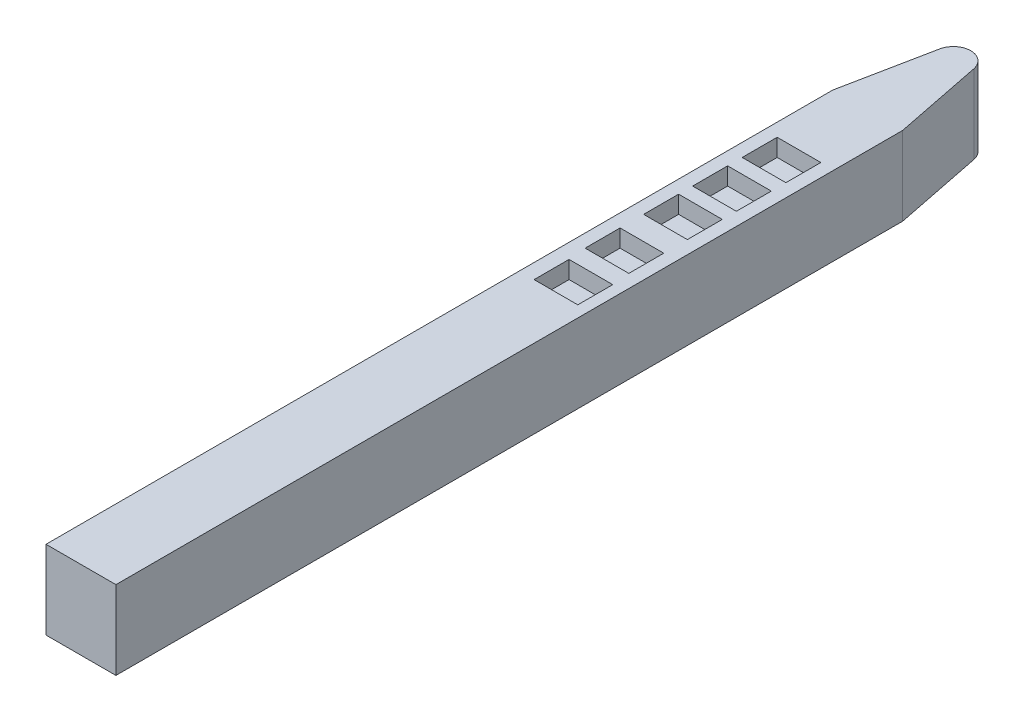
SolidWorks part; units mm, degrees
ref_plane "Front Plane" through (0, 0, 0) normal (0, 0, 1) x (1, 0, 0)
ref_plane "Top Plane" through (0, 0, 0) normal (0, 1, 0) x (1, 0, 0)
ref_plane "Right Plane" through (0, 0, 0) normal (1, 0, 0) x (0, 0, -1)
sketch "Sketch1" plane through (0, 0, 0) normal (0, 1, 0) x (1, 0, 0)
  line L0 (0, 0) -> (0, 1143.3615)
  line L1 (0, 0) -> (101.6, 0)
  line L2 (101.6, 0) -> (101.6, 1143.3615)
  line L3 (0, 1143.3615) -> (50.8, 1397)
  line L4 (50.8, 1397) -> (101.6, 1143.3615)
  line L5 (50.8, 0) -> (50.8, 1705.5122) construction
  dimension "D1" = 1397
  dimension "D2" = 101.6
extrude "Boss-Extrude1" add sketch "Sketch1" along normal blind 114.3
fillet "Fillet2" radius 25.4 1 edges at (50.8, 57.15, -1397)
sketch "Sketch2" plane through (0, 114.3, 0) normal (0, 1, 0) x (1, 0, 0)
  line L0 (50.8, 0) -> (50.8, 1195.0883) construction
  line L1 (0, 0) -> (101.6, 0) construction
  line L2 (19.05, 971.4743) -> (82.55, 971.4743)
  line L3 (19.05, 1043.4464) -> (82.55, 1043.4464)
  line L4 (19.05, 1043.4464) -> (19.05, 992.6464)
  line L5 (19.05, 992.6464) -> (82.55, 992.6464)
  line L6 (82.55, 1043.4464) -> (82.55, 992.6464)
  line L7 (19.05, 1043.4464) -> (82.55, 992.6464) construction
  line L8 (19.05, 992.6464) -> (82.55, 1043.4464) construction
  line L9 (19.05, 971.4743) -> (19.05, 920.6743)
  line L10 (19.05, 920.6743) -> (82.55, 920.6743)
  line L11 (82.55, 971.4743) -> (82.55, 920.6743)
  line L12 (19.05, 971.4743) -> (82.55, 920.6743) construction
  line L13 (19.05, 920.6743) -> (82.55, 971.4743) construction
  line L14 (19.05, 900.2229) -> (82.55, 900.2229)
  line L15 (19.05, 900.2229) -> (19.05, 849.4229)
  line L16 (19.05, 849.4229) -> (82.55, 849.4229)
  line L17 (82.55, 900.2229) -> (82.55, 849.4229)
  line L18 (19.05, 900.2229) -> (82.55, 849.4229) construction
  line L19 (19.05, 849.4229) -> (82.55, 900.2229) construction
  line L20 (19.05, 815.181) -> (82.55, 815.181)
  line L21 (19.05, 815.181) -> (19.05, 764.381)
  line L22 (19.05, 764.381) -> (82.55, 764.381)
  line L23 (82.55, 815.181) -> (82.55, 764.381)
  line L24 (19.05, 815.181) -> (82.55, 764.381) construction
  line L25 (19.05, 764.381) -> (82.55, 815.181) construction
  line L26 (21.5561, 738.5331) -> (85.0561, 738.5331)
  line L27 (21.5561, 738.5331) -> (21.5561, 687.7331)
  line L28 (21.5561, 687.7331) -> (85.0561, 687.7331)
  line L29 (85.0561, 738.5331) -> (85.0561, 687.7331)
  line L30 (21.5561, 738.5331) -> (85.0561, 687.7331) construction
  line L31 (21.5561, 687.7331) -> (85.0561, 738.5331) construction
  point P4 (50.8, 1018.0464)
  point P9 (50.8, 946.0743)
  point P14 (50.8, 874.8229)
  point P19 (50.8, 789.781)
  point P29 (53.3061, 713.1331)
  dimension "D1" = 63.5
  dimension "D2" = 50.8
  dimension "D3" = 63.5
  dimension "D4" = 50.8
  dimension "D5" = 63.5
  dimension "D6" = 50.8
  dimension "D7" = 63.5
  dimension "D8" = 50.8
  dimension "D9" = 63.5
  dimension "D10" = 50.8
extrude "Cut-Extrude1" cut sketch "Sketch2" against normal blind 25.4
ref_plane "Plane1" through (50.8, 0, 0) normal (1, 0, 0) x (0, 0, -1)
